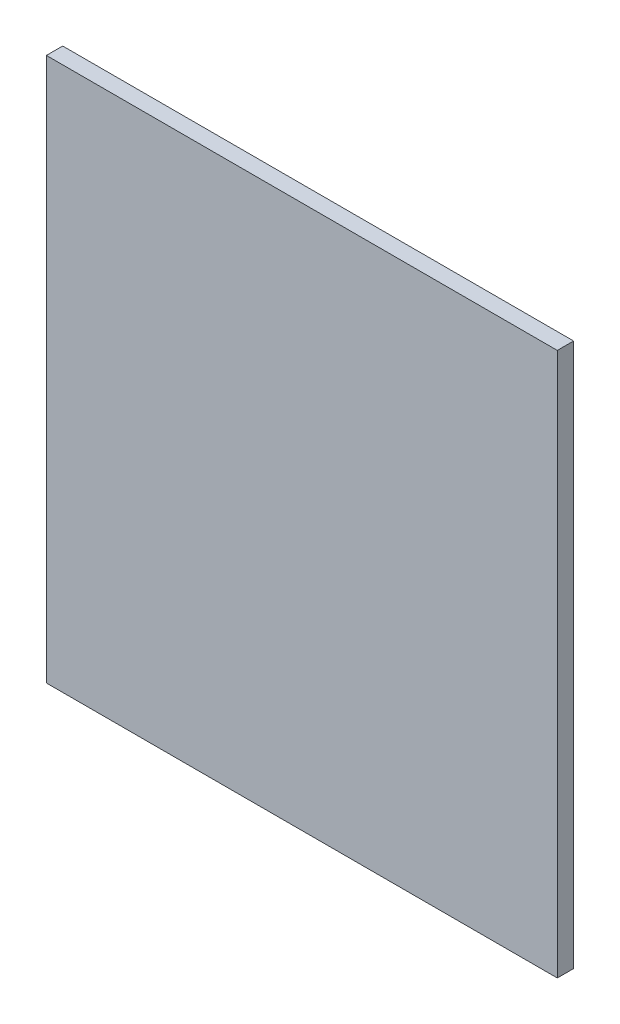
SolidWorks part; units mm, degrees
ref_plane "Спереди" through (0, 0, 0) normal (0, 0, 1) x (1, 0, 0)
ref_plane "Сверху" through (0, 0, 0) normal (0, 1, 0) x (1, 0, 0)
ref_plane "Справа" through (0, 0, 0) normal (1, 0, 0) x (0, 0, -1)
sketch "Эскиз1" plane through (0, 0, 0) normal (0, 0, 1) x (1, 0, 0)
  line L1 (-282, 300) -> (282, 300)
  line L2 (-282, 300) -> (-282, -300)
  line L3 (-282, -300) -> (282, -300)
  line L4 (282, 300) -> (282, -300)
  line L5 (-282, 300) -> (282, -300) construction
  line L6 (-282, -300) -> (282, 300) construction
  point P0 (0, 0)
extrude "Бобышка-Вытянуть1" add sketch "Эскиз1" along normal blind 18
